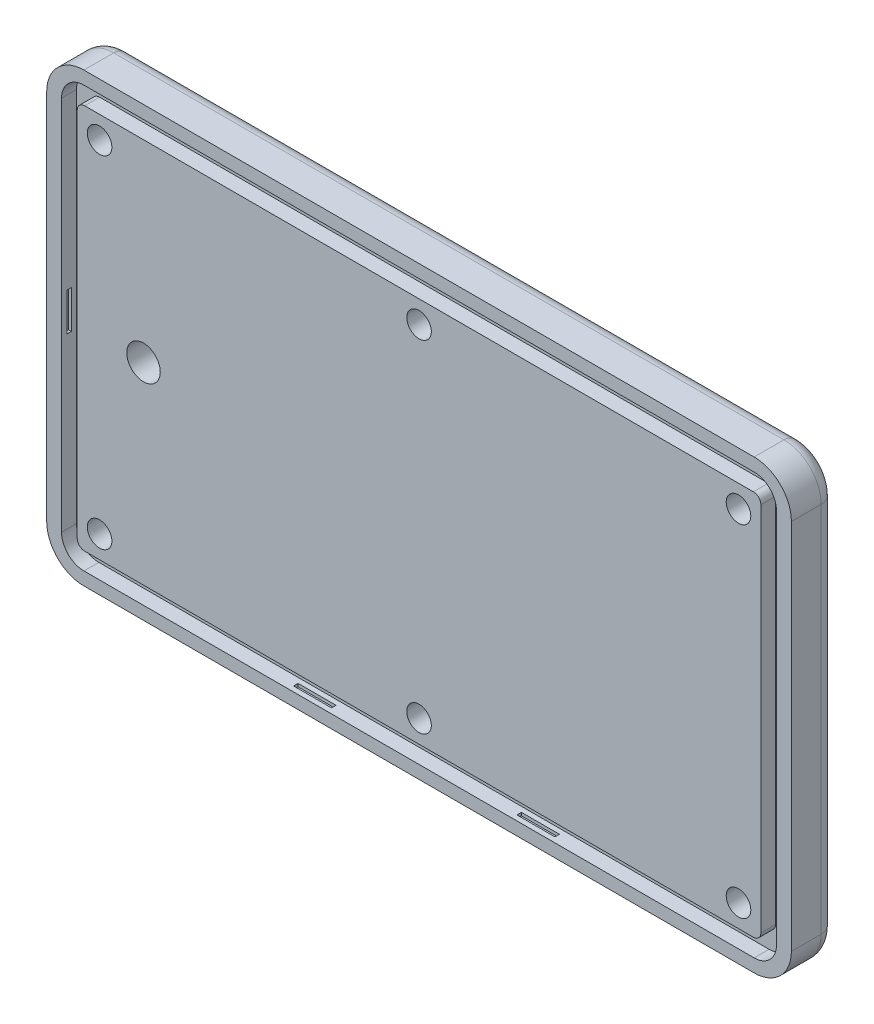
SolidWorks part; units mm, degrees
ref_plane "前视基准面" through (0, 0, 0) normal (0, 0, 1) x (1, 0, 0)
ref_plane "上视基准面" through (0, 0, 0) normal (0, 1, 0) x (1, 0, 0)
ref_plane "右视基准面" through (0, 0, 0) normal (1, 0, 0) x (0, 0, -1)
other "Configuration Table"
sketch "草图1" plane through (0, 0, 0) normal (0, 0, 1) x (1, 0, 0)
  line L1 (50, 30) -> (-50, 30)
  line L2 (50, 30) -> (50, -30)
  line L3 (50, -30) -> (-50, -30)
  line L4 (-50, 30) -> (-50, -30)
  line L5 (50, 30) -> (-50, -30) construction
  line L6 (50, -30) -> (-50, 30) construction
  point P0 (0, 0)
  dimension "D1" = 100
  dimension "D2" = 60
extrude "凸台-拉伸1" add sketch "草图1" along normal blind 6
fillet "圆角1" radius 5 4 edges at (-50, -30, 3) (50, -30, 3) (50, 30, 3) (-50, 30, 3)
fillet "圆角2" radius 2 8 edges at (48.5355, -28.5355, 0) (50, 0, 0) (48.5355, 28.5355, 0) (0, 30, 0) (-48.5355, 28.5355, 0) (-50, 0, 0) (-48.5355, -28.5355, 0) (0, -30, 0)
sketch "草图2" plane through (0, 0, 6) normal (0, 0, 1) x (1, 0, 0)
  line L1 (-45, 28.25) -> (45, 28.25)
  line L2 (-48, 25.25) -> (-48, -25.25)
  line L3 (-45, -28.25) -> (45, -28.25)
  line L4 (48, 25.25) -> (48, -25.25)
  line L5 (-48, 28.25) -> (48, -28.25) construction
  line L6 (-48, -28.25) -> (48, 28.25) construction
  arc A0 (45, -28.25) -> (48, -25.25) centre (45, -25.25) ccw
  arc A1 (48, 25.25) -> (45, 28.25) centre (45, 25.25) ccw
  arc A2 (-45, 28.25) -> (-48, 25.25) centre (-45, 25.25) ccw
  arc A3 (-45, -28.25) -> (-48, -25.25) centre (-45, -25.25) cw
  point P0 (0, 0)
  dimension "D1" = 3
  dimension "D2" = 96
  dimension "D3" = 56.5
extrude "切除-拉伸1" cut sketch "草图2" against normal blind 2
sketch "草图4" plane through (0, -28.25, 0) normal (0, 1, 0) x (1, 0, 0)
  line L0 (45, -5) -> (-45, -5) construction
  line L1 (17.55, -5.3) -> (12.45, -5.3)
  line L2 (17.55, -5.3) -> (17.55, -4.7)
  line L3 (17.55, -4.7) -> (12.45, -4.7)
  line L4 (12.45, -5.3) -> (12.45, -4.7)
  line L5 (17.55, -5.3) -> (12.45, -4.7) construction
  line L6 (17.55, -4.7) -> (12.45, -5.3) construction
  line L10 (-12.45, -5.3) -> (-17.55, -5.3)
  line L11 (-12.45, -5.3) -> (-12.45, -4.7)
  line L12 (-12.45, -4.7) -> (-17.55, -4.7)
  line L13 (-17.55, -5.3) -> (-17.55, -4.7)
  line L14 (-12.45, -5.3) -> (-17.55, -4.7) construction
  line L15 (-12.45, -4.7) -> (-17.55, -5.3) construction
  line L16 (45, -6) -> (45, -2) construction
  line L17 (-45, -2) -> (-45, -6) construction
  line L18 (45, -6) -> (-45, -6) construction
  point P0 (15, -5)
  point P12 (-15, -5)
  dimension "D1" = 1
  dimension "D2" = 0.6
  dimension "D3" = 5.1
  dimension "D4" = 0.6
  dimension "D5" = 5.1
  dimension "D6" = 30
  dimension "D7" = 60
extrude "切除-拉伸2" cut sketch "草图4" against normal blind 0.4
sketch "草图5" plane through (0, 28.25, 0) normal (0, -1, 0) x (1, 0, 0)
  line L0 (-17.55, 5.3) -> (-17.55, 4.7) construction
  line L1 (-12.45, 5.3) -> (-17.55, 5.3) construction
  line L2 (-12.45, 4.7) -> (-17.55, 4.7) construction
  line L3 (-12.45, 5.3) -> (-12.45, 4.7) construction
  line L4 (12.45, 5.3) -> (12.45, 4.7) construction
  line L5 (17.55, 5.3) -> (12.45, 5.3) construction
  line L6 (17.55, 5.3) -> (17.55, 4.7) construction
  line L7 (17.55, 4.7) -> (12.45, 4.7) construction
  line L8 (-17.55, 5.3) -> (-17.55, 4.7)
  line L9 (-12.45, 5.3) -> (-17.55, 5.3)
  line L10 (-12.45, 4.7) -> (-17.55, 4.7)
  line L11 (-12.45, 5.3) -> (-12.45, 4.7)
  line L12 (12.45, 5.3) -> (12.45, 4.7)
  line L13 (17.55, 5.3) -> (12.45, 5.3)
  line L14 (17.55, 5.3) -> (17.55, 4.7)
  line L15 (17.55, 4.7) -> (12.45, 4.7)
extrude "切除-拉伸3" cut sketch "草图5" against normal blind 0.4
sketch "草图6" plane through (-48, 0, 0) normal (1, 0, 0) x (0, 0, -1)
  line L0 (-6, -25) -> (-2, -25) construction
  line L1 (-5, -25) -> (-5, 25) construction
  line L2 (-2, 25) -> (-6, 25) construction
  line L3 (-6, -25) -> (-6, 25) construction
  line L5 (-5.3, -2.55) -> (-4.7, -2.55)
  line L6 (-5.3, -2.55) -> (-5.3, 2.55)
  line L7 (-5.3, 2.55) -> (-4.7, 2.55)
  line L8 (-4.7, -2.55) -> (-4.7, 2.55)
  line L9 (-5.3, -2.55) -> (-4.7, 2.55) construction
  line L10 (-5.3, 2.55) -> (-4.7, -2.55) construction
  point P8 (-5, 0)
  point P15 (-5, 0)
  dimension "D1" = 1
  dimension "D2" = 5.1
  dimension "D3" = 0.6
extrude "切除-拉伸4" cut sketch "草图6" against normal blind 0.4
sketch "草图7" plane through (48, 0, 0) normal (-1, 0, 0) x (0, 0, 1)
  line L0 (5.3, 2.55) -> (4.7, 2.55) construction
  line L1 (5.3, -2.55) -> (4.7, -2.55) construction
  line L2 (5.3, -2.55) -> (5.3, 2.55) construction
  line L3 (4.7, -2.55) -> (4.7, 2.55) construction
  line L4 (5.3, 2.55) -> (4.7, 2.55)
  line L5 (5.3, -2.55) -> (4.7, -2.55)
  line L6 (5.3, -2.55) -> (5.3, 2.55)
  line L7 (4.7, -2.55) -> (4.7, 2.55)
extrude "切除-拉伸5" cut sketch "草图7" against normal blind 0.4
sketch "草图8" plane through (0, 0, 4) normal (0, 0, 1) x (1, 0, 0)
  line L1 (44.9, -25.9) -> (-44.9, -25.9)
  line L2 (45.9, -24.9) -> (45.9, 24.9)
  line L3 (44.9, 25.9) -> (-44.9, 25.9)
  line L4 (-45.9, -24.9) -> (-45.9, 24.9)
  line L5 (45.9, -25.9) -> (-45.9, 25.9) construction
  line L6 (45.9, 25.9) -> (-45.9, -25.9) construction
  arc A0 (-45.9, 24.9) -> (-44.9, 25.9) centre (-44.9, 24.9) cw
  arc A1 (-45.9, -24.9) -> (-44.9, -25.9) centre (-44.9, -24.9) ccw
  arc A2 (45.9, -24.9) -> (44.9, -25.9) centre (44.9, -24.9) cw
  arc A3 (44.9, 25.9) -> (45.9, 24.9) centre (44.9, 24.9) cw
  point P0 (0, 0)
  dimension "D3" = 1
  dimension "D1" = 91.8
  dimension "D2" = 51.8
extrude "凸台-拉伸2" add sketch "草图8" along normal blind 2
sketch "草图9" plane through (0, 0, 6) normal (0, 0, 1) x (1, 0, 0)
  line L0 (45.9, -24.9) -> (45.9, 24.9) construction
  line L1 (44.9, 25.9) -> (-44.9, 25.9) construction
  line L2 (0, 2.2273) -> (0, 28.2273) construction
  line L4 (0, 0) -> (46, 0) construction
  circle A0 centre (42.9, 22.9) radius 1.65
  circle A1 centre (0, 22.9) radius 1.65
  circle A2 centre (-42.9, 22.9) radius 1.65
  circle A3 centre (-42.9, -22.9) radius 1.65
  circle A4 centre (0, -22.9) radius 1.65
  circle A5 centre (42.9, -22.9) radius 1.65
  dimension "D1" = 3.3
  dimension "D4" = 3.3
  dimension "D2" = 3
  dimension "D3" = 3
  dimension "D5" = 3
extrude "切除-拉伸6" cut sketch "草图9" against normal up to next
sketch "草图10" plane through (0, 0, 0) normal (0, 0, -1) x (-1, 0, 0)
  circle A0 centre (42.9, 22.9) radius 3.05
  circle A1 centre (0, 22.9) radius 3.05
  circle A2 centre (-42.9, 22.9) radius 3.05
  circle A3 centre (-42.9, -22.9) radius 3.05
  circle A4 centre (0, -22.9) radius 3.05
  circle A5 centre (42.9, -22.9) radius 3.05
  dimension "D1" = 6.1
extrude "切除-拉伸7" cut sketch "草图10" against normal blind 1.1
fillet "圆角3" radius 0.5 6 edges at (39.85, 22.9, 0) (39.85, -22.9, 0) (-3.05, -22.9, 0) (-3.05, 22.9, 0) (-45.95, -22.9, 0) (-45.95, 22.9, 0)
sketch "草图11" plane through (0, 0, 6) normal (0, 0, 1) x (1, 0, 0)
  line L0 (-200000, 0) -> (200046, 0) construction
  line L1 (-48, 25.25) -> (-48, -25.25) construction
  circle A0 centre (-37, 0) radius 2.25
  point P4 (0, 0)
  dimension "D1" = 4.5
  dimension "D2" = 11
extrude "切除-拉伸8" cut sketch "草图11" against normal up to next
